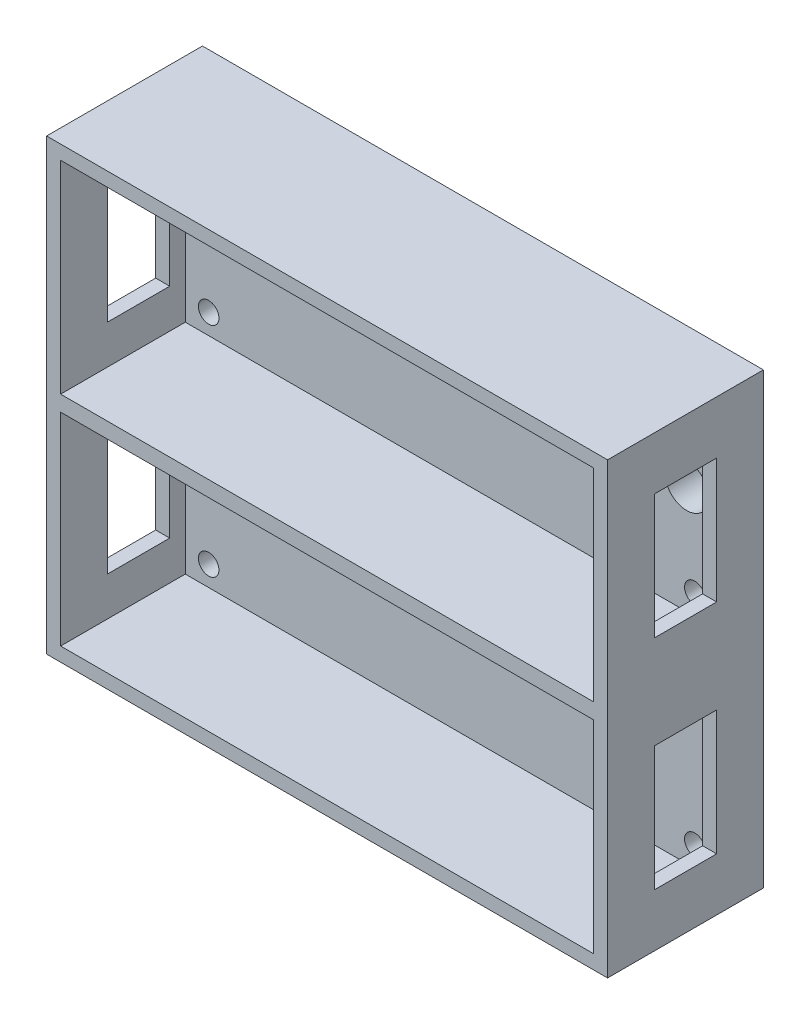
SolidWorks part; units mm, degrees
material "ABS"
ref_plane "前视基准面" through (0, 0, 0) normal (0, 0, 1) x (1, 0, 0)
ref_plane "上视基准面" through (0, 0, 0) normal (0, 1, 0) x (1, 0, 0)
ref_plane "右视基准面" through (0, 0, 0) normal (1, 0, 0) x (0, 0, -1)
other "Configuration Table"
sketch "草图1" plane through (0, 0, 0) normal (0, 0, 1) x (1, 0, 0)
  line L1 (-45, -36) -> (45, -36)
  line L2 (-45, -36) -> (-45, 36)
  line L3 (-45, 36) -> (45, 36)
  line L4 (45, -36) -> (45, 36)
  line L5 (-45, -36) -> (45, 36) construction
  line L6 (-45, 36) -> (45, -36) construction
  point P0 (0, 0)
  dimension "D1" = 72
  dimension "D2" = 90
extrude "凸台-拉伸1" add sketch "草图1" along normal blind 25
sketch "草图2" plane through (0, 0, 25) normal (0, 0, 1) x (1, 0, 0)
  line L1 (-42.75, 1.25) -> (42.75, 1.25)
  line L2 (-42.75, 1.25) -> (-42.75, 33.75)
  line L3 (-42.75, 33.75) -> (42.75, 33.75)
  line L4 (42.75, 1.25) -> (42.75, 33.75)
  line L5 (-42.75, 1.25) -> (42.75, 33.75) construction
  line L6 (-42.75, 33.75) -> (42.75, 1.25) construction
  line L7 (-42.75, -33.75) -> (42.75, -33.75)
  line L8 (-42.75, -33.75) -> (-42.75, -1.25)
  line L9 (-42.75, -1.25) -> (42.75, -1.25)
  line L10 (42.75, -33.75) -> (42.75, -1.25)
  line L11 (-42.75, -33.75) -> (42.75, -1.25) construction
  line L12 (-42.75, -1.25) -> (42.75, -33.75) construction
  point P0 (0, 17.5)
  point P5 (0, -17.5)
  dimension "D1" = 2.5
  dimension "D2" = 1.25
  dimension "D3" = 85.5
  dimension "D4" = 67.5
extrude "切除-拉伸1" cut sketch "草图2" against normal blind 20
sketch "草图3" plane through (45, 0, 0) normal (1, 0, 0) x (0, 0, -1)
  line L0 (0, 0) -> (-25, 0) construction
  line L1 (-17.5, 7.5) -> (-7.5, 7.5)
  line L2 (-17.5, 7.5) -> (-17.5, 27.5)
  line L3 (-17.5, 27.5) -> (-7.5, 27.5)
  line L4 (-7.5, 7.5) -> (-7.5, 27.5)
  line L5 (-17.5, 7.5) -> (-7.5, 27.5) construction
  line L6 (-17.5, 27.5) -> (-7.5, 7.5) construction
  line L7 (-17.5, -27.5) -> (-7.5, -27.5)
  line L8 (-17.5, -27.5) -> (-17.5, -7.5)
  line L9 (-17.5, -7.5) -> (-7.5, -7.5)
  line L10 (-7.5, -27.5) -> (-7.5, -7.5)
  line L11 (-17.5, -27.5) -> (-7.5, -7.5) construction
  line L12 (-17.5, -7.5) -> (-7.5, -27.5) construction
  line L13 (-25, -36) -> (-25, 36) construction
  point P0 (-12.5, 17.5)
  point P5 (-12.5, -17.5)
  point P15 (0, 0)
  point P16 (-12.5, 0)
  dimension "D1" = 20
  dimension "D2" = 10
  dimension "D3" = 35
extrude "切除-拉伸2" cut sketch "草图3" against normal through all both and the other way through all
sketch "草图4" plane through (0, 0, 5) normal (0, 0, 1) x (1, 0, 0)
  circle A0 centre (-39, 4.5) radius 1.65
  circle A1 centre (-39, 30.5) radius 1.65
  circle A2 centre (-39, -4.5) radius 1.65
  circle A3 centre (-39, -30.5) radius 1.65
  circle A4 centre (39, -30.5) radius 1.65
  circle A5 centre (39, -4.5) radius 1.65
  circle A6 centre (39, 4.5) radius 1.65
  circle A7 centre (39, 30.5) radius 1.65
  dimension "D1" = 3.3
extrude "切除-拉伸3" cut sketch "草图4" against normal through all both
sketch "草图5" plane through (0, 0, 0) normal (0, 0, -1) x (-1, 0, 0)
  line L0 (-45, 36) -> (45, 36) construction
  line L1 (-45, -36) -> (-45, 36) construction
  circle A0 centre (-37.7, 18.8) radius 3.5
  point P2 (-37.7, 18.8)
  point P3 (0, 0)
  dimension "D1" = 7
  dimension "D2" = 17.2
  dimension "D3" = 7.3
extrude "切除-拉伸4" cut sketch "草图5" against normal through all both and the other way through all
